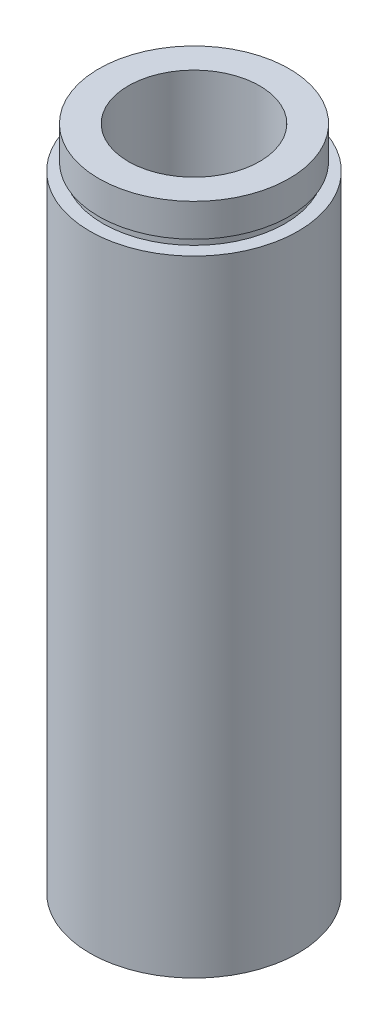
SolidWorks part; units mm, degrees
ref_plane "前视基准面" through (0, 0, 0) normal (0, 0, 1) x (1, 0, 0)
ref_plane "上视基准面" through (0, 0, 0) normal (0, 1, 0) x (1, 0, 0)
ref_plane "右视基准面" through (0, 0, 0) normal (1, 0, 0) x (0, 0, -1)
sketch "草图1" plane through (0, 0, 0) normal (0, 0, 1) x (1, 0, 0)
  line L0 (0, 161.3762) -> (0, 0) construction
  line L1 (141.7365, 0) -> (-131.7984, 0) construction
  line L2 (11.1, 0) -> (11.1, 4.5)
  line L3 (11.7, 4.5) -> (11.7, 5.5)
  line L4 (11.1, 4.5) -> (11.7, 4.5)
  line L5 (8, 5.5) -> (8, 81.2)
  line L6 (11.7, 5.5) -> (8, 5.5)
  line L7 (12.7, 0) -> (12.7, 76.2)
  line L8 (11.1, 0) -> (12.7, 0)
  line L9 (11.1, 76.2) -> (11.1, 77.2)
  line L10 (12.7, 76.2) -> (11.1, 76.2)
  line L11 (11.6, 77.2) -> (11.6, 81.2)
  line L12 (11.1, 77.2) -> (11.6, 77.2)
  line L13 (11.6, 81.2) -> (8, 81.2)
  point P12 (8, 81.5721)
  dimension "D1" = 11.1
  dimension "D2" = 4.5
  dimension "D3" = 11.7
  dimension "D4" = 8
  dimension "D5" = 11.1
  dimension "D6" = 11.6
  dimension "D7" = 5
  dimension "D8" = 1
  dimension "D9" = 12.7
  dimension "D10" = 1
  dimension "D11" = 76.2
revolve "旋转1" add sketch "草图1" angle 360 about L0
cosmetic thread "装饰螺纹线1"
cosmetic thread "装饰螺纹线2"
cosmetic thread "装饰螺纹线3"
